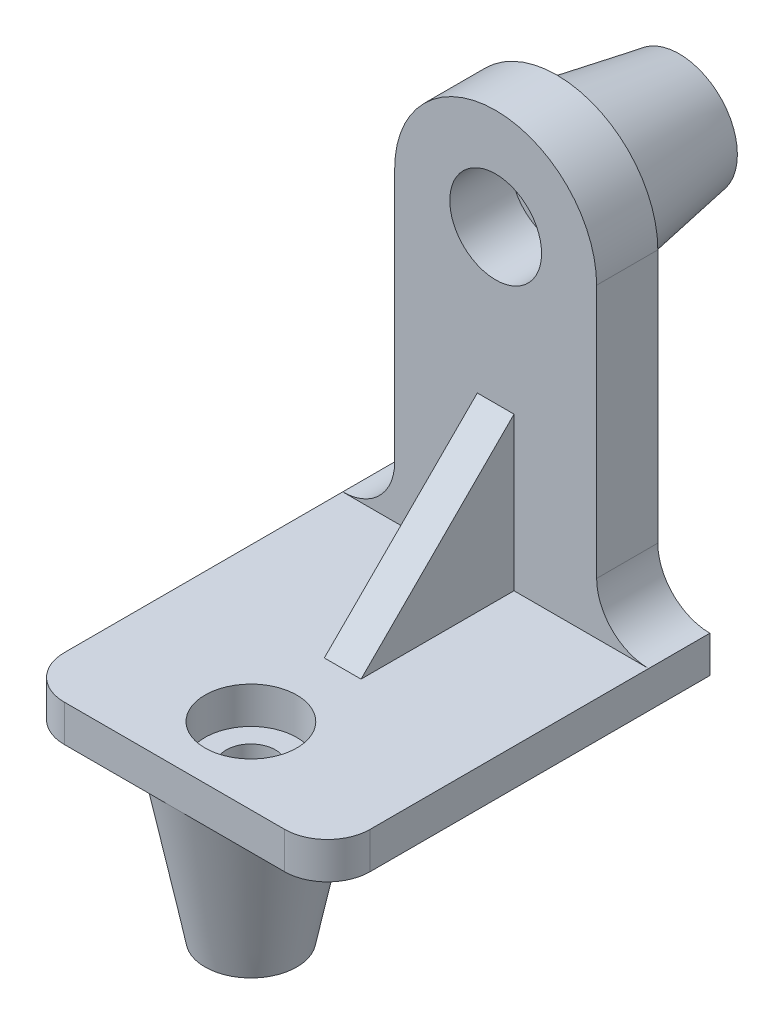
SolidWorks part; units mm, degrees
ref_plane "Alzado" through (0, 0, 0) normal (0, 0, 1) x (1, 0, 0)
ref_plane "Planta" through (0, 0, 0) normal (0, 1, 0) x (1, 0, 0)
ref_plane "Vista lateral" through (0, 0, 0) normal (1, 0, 0) x (0, 0, -1)
sketch "Croquis1" plane through (0, 0, 0) normal (0, 0, 1) x (1, 0, 0)
  line L0 (-50, 0) -> (50, 0)
  line L1 (33, 17) -> (33, 100)
  line L2 (-33, 100) -> (-33, 17)
  arc A0 (50, 0) -> (33, 17) centre (50, 17) cw
  arc A1 (33, 100) -> (-33, 100) centre (0, 100) ccw
  arc A2 (-33, 17) -> (-50, 0) centre (-50, 17) cw
  circle A3 centre (0, 100) radius 15
  point P4 (0, 0)
  dimension "D2" = 17
  dimension "D4" = 30
  dimension "D1" = 100
  dimension "D3" = 100
extrude "Saliente-Extruir1" add sketch "Croquis1" against normal blind 20
sketch "Croquis2" plane through (0, 0, 0) normal (0, 1, 0) x (1, 0, 0)
  line L0 (-50, 20) -> (-50, -91)
  line L1 (-36, -105) -> (36, -105)
  line L2 (50, -91) -> (50, 20)
  line L3 (50, 20) -> (-50, 20)
  arc A0 (36, -105) -> (50, -91) centre (36, -91) ccw
  arc A1 (-50, -91) -> (-36, -105) centre (-36, -91) ccw
  circle A2 centre (0, -80) radius 15
  point P9 (50, -105)
  point P14 (0, 0)
  point P16 (0, -84.0187)
  dimension "D2" = 14
  dimension "D3" = 30
  dimension "D1" = 125
  dimension "D4" = 25
extrude "Saliente-Extruir2" add sketch "Croquis2" against normal blind 12
sketch "Croquis3" plane through (0, 0, 0) normal (1, 0, 0) x (0, 0, -1)
  line L0 (0, 50) -> (-50, 0)
  line L1 (0, 17) -> (0, 100) construction
  line L2 (-91, 0) -> (0, 0) construction
  line L3 (-50, 0) -> (0, 0)
  line L4 (0, 0) -> (0, 50)
  dimension "D1" = 50
extrude "Saliente-Extruir3" add sketch "Croquis3" along normal mid plane 12
sketch "Croquis5" plane through (0, 0, 0) normal (1, 0, 0) x (0, 0, -1)
  line L0 (0, 100) -> (101.3166, 100) construction
  line L2 (20, 126) -> (60, 119)
  line L3 (20, 100) -> (20, 133) construction
  line L4 (60, 119) -> (60, 110)
  line L5 (60, 110) -> (20, 110)
  line L6 (20, 85) -> (20, 115) construction
  line L7 (20, 126) -> (20, 110)
  dimension "D1" = 52
  dimension "D2" = 40
  dimension "D3" = 38
  dimension "D4" = 20
revolve "Revolución1" add sketch "Croquis5" angle 360 about L0
sketch "Croquis6" plane through (0, 0, 0) normal (1, 0, 0) x (0, 0, -1)
  line L0 (-105, -12) -> (-95, -62)
  line L1 (-95, -62) -> (-88, -62)
  line L2 (-88, -62) -> (-88, -12)
  line L3 (-88, -12) -> (-105, -12)
  line L4 (-95, -12) -> (-65, -12) construction
  line L5 (-80, -12) -> (-80, -119.68) construction
  line L7 (-95, -12) -> (-65, -12) construction
  point P8 (-80, -12)
  point P9 (0, 0)
  point P10 (-68.1476, -12)
  dimension "D1" = 30
  dimension "D2" = 16
  dimension "D3" = 50
revolve "Revolución2" add sketch "Croquis6" angle 360 about L5
